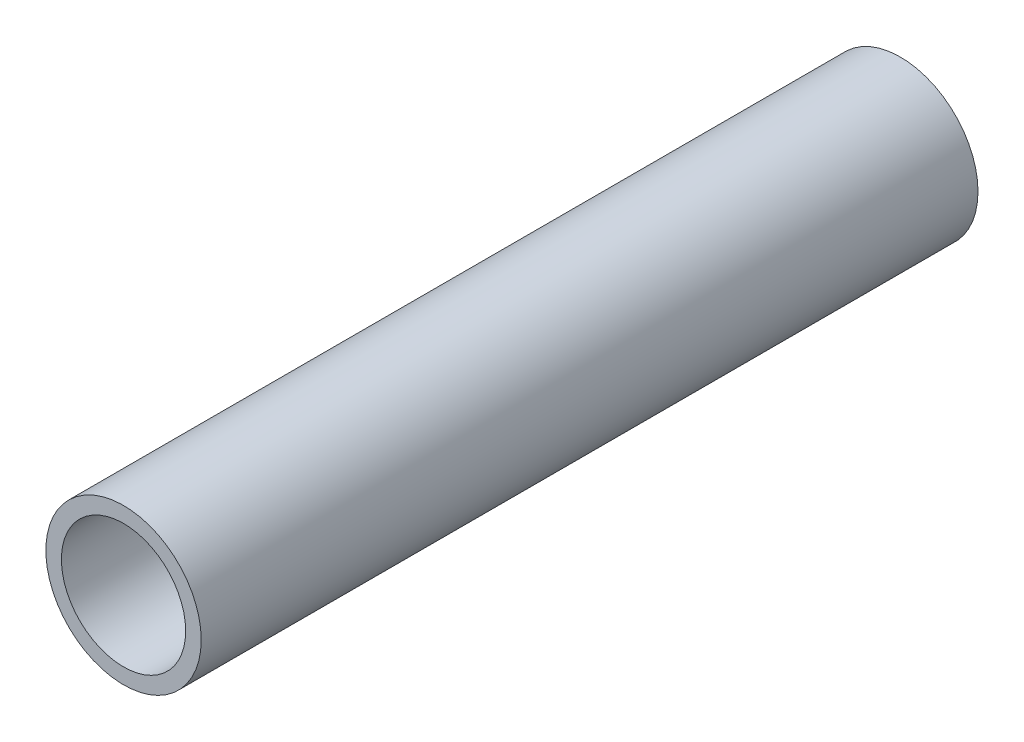
SolidWorks part; units mm, degrees
ref_plane "Front Plane" through (0, 0, 0) normal (0, 0, 1) x (1, 0, 0)
ref_plane "Top Plane" through (0, 0, 0) normal (0, 1, 0) x (1, 0, 0)
ref_plane "Right Plane" through (0, 0, 0) normal (1, 0, 0) x (0, 0, -1)
sketch "Sketch1" plane through (0, 0, 0) normal (0, 0, 1) x (1, 0, 0)
  circle A0 centre (0, 0) radius 12.7
  dimension "D1" = 25.4
extrude "Extrude-Thin1" add sketch "Sketch1" along normal blind 127 thin thin type one direction reverse wall 2.54
